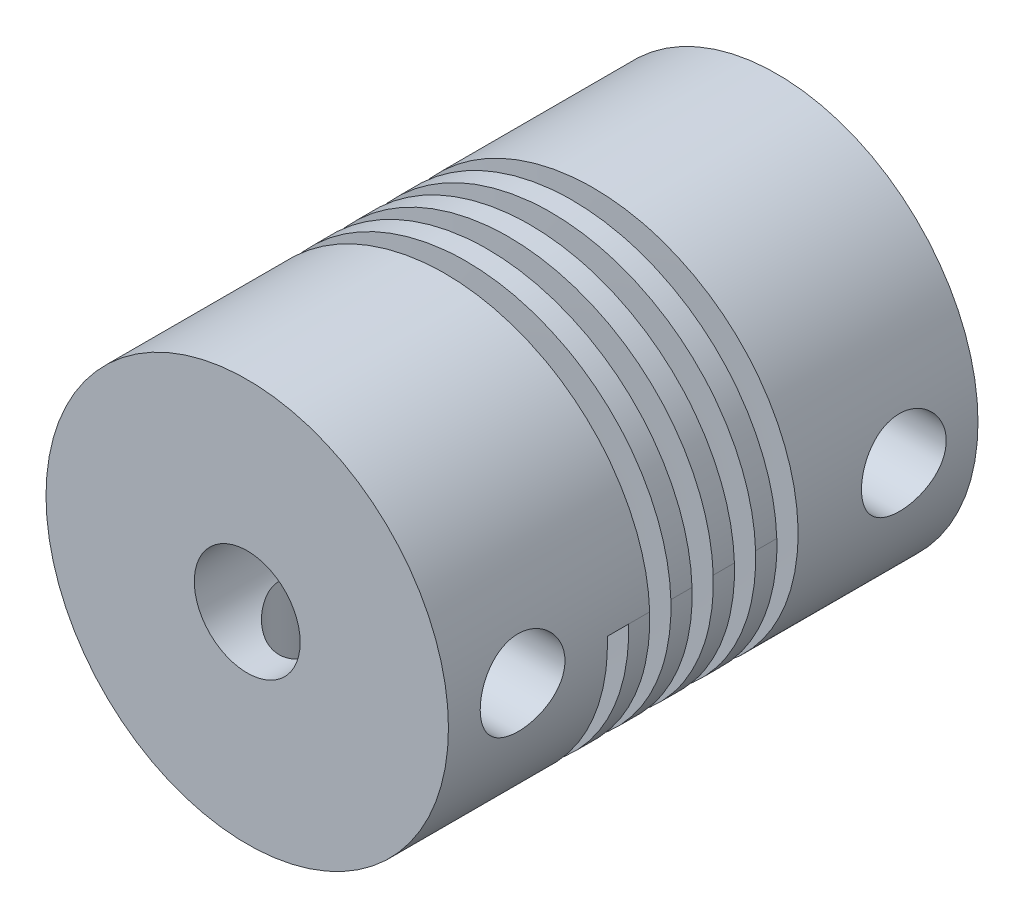
SolidWorks part; units mm, degrees
ref_plane "Front Plane" through (0, 0, 0) normal (0, 0, 1) x (1, 0, 0)
ref_plane "Top Plane" through (0, 0, 0) normal (0, 1, 0) x (1, 0, 0)
ref_plane "Right Plane" through (0, 0, 0) normal (1, 0, 0) x (0, 0, -1)
sketch "Sketch1" plane through (0, 0, 0) normal (0, 0, 1) x (1, 0, 0)
  circle A0 centre (0, 0) radius 9.5
  circle A1 centre (0, 0) radius 4
  dimension "D1" = 19
  dimension "D2" = 8
extrude "Boss-Extrude1" add sketch "Sketch1" along normal blind 25
sketch "Sketch2" plane through (0, 0, 25) normal (0, 0, 1) x (1, 0, 0)
  circle A0 centre (0, 0) radius 4
  circle A1 centre (0, 0) radius 2.5
  dimension "D1" = 5
  dimension "D2" = 8
extrude "Boss-Extrude2" add sketch "Sketch2" against normal blind 12.5
sketch "Sketch3" plane through (0, 0, 0) normal (0, 1, 0) x (1, 0, 0)
  line L0 (9.5, 0) -> (-9.5, 0) construction
  line L1 (-9.5, -25) -> (9.5, -25) construction
  circle A0 centre (0, -3.5) radius 2
  circle A1 centre (0, -21.5) radius 2
  dimension "D1" = 4
  dimension "D2" = 4
  dimension "D3" = 3.5
  dimension "D4" = 3.5
extrude "Cut-Extrude1" cut sketch "Sketch3" against normal blind 12.5
pattern_circular "CirPattern1" count 2 every 90 about axis through (0, 0, 25) along (0, 0, -1) of "Cut-Extrude1"
ref_plane "Plane1" through (0, 0, 8) normal (0, 0, -1) x (-1, 0, 0)
sketch "Sketch4" plane through (0, 0, 8) normal (0, 0, -1) x (-1, 0, 0)
  circle A1 centre (0, 0) radius 9.5
  circle A2 centre (0, 0) radius 9.5
  dimension "D1" = 0
sketch "Sketch5" plane through (0, 0, 0) normal (0, 1, 0) x (1, 0, 0)
  line L2 (9.5, -8) -> (-9.5, -8) construction
  line L3 (-14.5, -7.5) -> (-4.5, -7.5)
  line L4 (-14.5, -7.5) -> (-14.5, -8.5)
  line L5 (-14.5, -8.5) -> (-4.5, -8.5)
  line L6 (-4.5, -7.5) -> (-4.5, -8.5)
  line L7 (-14.5, -7.5) -> (-4.5, -8.5) construction
  line L8 (-14.5, -8.5) -> (-4.5, -7.5) construction
  line L9 (10.45, -8) -> (-10.45, -8) construction
  point P0 (-9.5, -8)
  point P9 (0, 0)
  dimension "D1" = 1
  dimension "D2" = 10
curve "Helix/Spiral1" pitch 2 height 9 turns 4.5
sweep "Cut-Sweep1" cut profiles "Sketch5" path "Helix/Spiral1"
